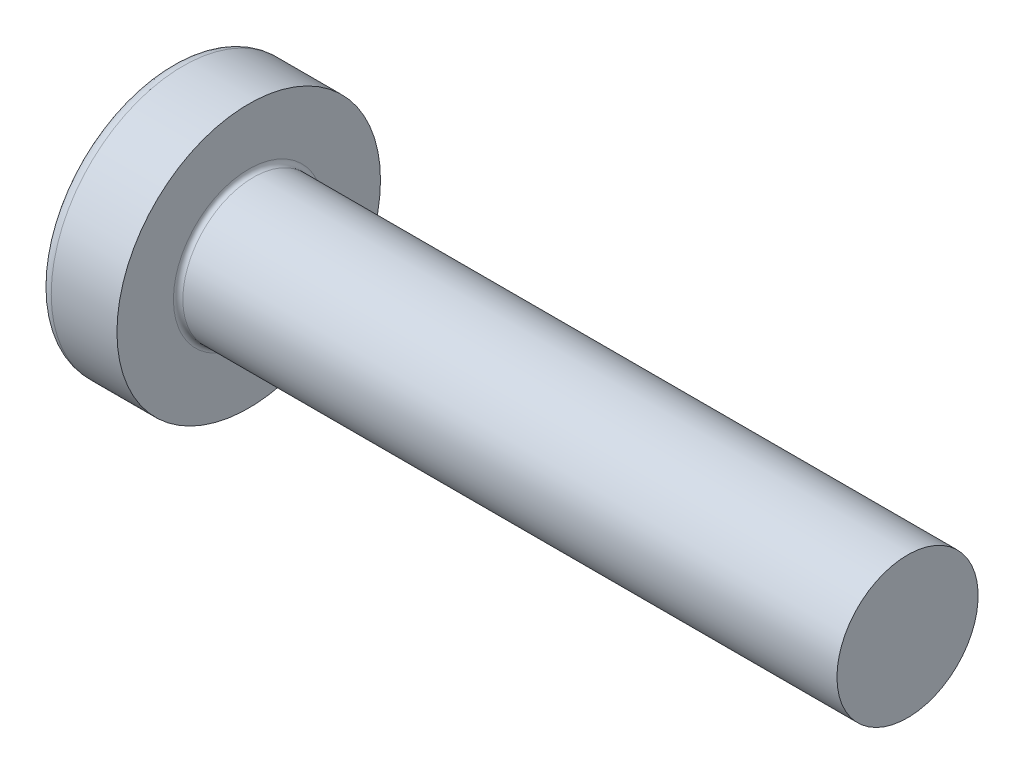
SolidWorks part; units mm, degrees
ref_plane "Plane1" through (0, 0, 0) normal (0, 0, 1) x (1, 0, 0)
ref_plane "Plane2" through (0, 0, 0) normal (0, 1, 0) x (1, 0, 0)
ref_plane "Plane3" through (0, 0, 0) normal (1, 0, 0) x (0, 0, -1)
sketch "BodySke" plane through (0, 0, 0) normal (0, 0, 1) x (1, 0, 0)
  line L0 (2.4, 1.5) -> (2.4, 2.8)
  line L1 (2.65, 6.35) -> (2.65, -3.175) construction
  line L2 (-25.4, 0) -> (127, 0) construction
  line L3 (16.4, 0) -> (0, 0)
  line L4 (2.4, 1.5) -> (16.4, 1.5)
  line L5 (16.4, 1.5) -> (16.4, 0)
  line L6 (1.0035, 2.8) -> (2.4, 2.8)
  line L8 (0.4, 6.35) -> (0.4, -3.175) construction
  arc A0 (0.7754, 2.6744) -> (0, 0) centre (5, 0) ccw
  arc A2 (0.7754, 2.6744) -> (1.0035, 2.8) centre (1.0035, 2.53) cw
  dimension "Head_crown_rad" = 5
  dimension "Head_fillet_rad" = 0.27
  dimension "Length" = 14
  dimension "Head_ht" = 2.4
  dimension "Head_dia" = 5.6
  dimension "Advance" = 0.5
  dimension "Thread_nom" = 16
  dimension "Diameter" = 3
revolve "Base-Revolve" add sketch "BodySke"
cosmetic thread "ThreadCosmetic" [suppressed]
fillet "Fillet1" radius 0.1 1 edges at (2.4, 0, 1.5)
sketch "Sketch3" plane through (0, 0, 0) normal (1, 0, 0) x (0, 0, -1)
  line L0 (0.37, -1.4) -> (-0.37, -1.4)
  line L1 (0.37, -1.4) -> (0.37, 1.4)
  line L2 (-0.37, 1.4) -> (0.37, 1.4)
  line L3 (-0.37, 1.4) -> (-0.37, -1.4)
  dimension "Cross_dia" = 2.8
  dimension "D1" = 1.4
  dimension "Cross_width" = 0.74
  dimension "D2" = 0.37
ref_plane "Plane4" through (1.75, 0, 0) normal (1, 0, 0) x (0, 0, -1)
sketch "Sketch4" plane through (1.75, 0, 0) normal (1, 0, 0) x (0, 0, -1)
  line L0 (0.37, -0.5275) -> (-0.37, -0.5275)
  line L1 (0.37, -0.5275) -> (0.37, 0.5275)
  line L2 (-0.37, 0.5275) -> (0.37, 0.5275)
  line L3 (-0.37, 0.5275) -> (-0.37, -0.5275)
  dimension "D1" = 0.74
  dimension "D2" = 1.055
  dimension "D3" = 0.37
  dimension "D4" = 0.5275
loft "Recess" cut profiles "Sketch3", "Sketch4"
pattern_circular "RecPat" count 2 every 90 about axis through (0, 0, 0) along (1, 0, 0) of "Recess"
sketch "RecCorSke" plane through (0, 0, 0) normal (0, 0, 1) x (1, 0, 0)
  line L0 (-3.175, 0) -> (15.875, 0) construction
  line L1 (-25.4, 0) -> (127, 0) construction
  line L2 (0, 0) -> (0, 0.6784)
  line L3 (0, 0.6784) -> (1.75, 0.556)
  line L4 (1.75, 0.556) -> (1.9307, 0)
  line L5 (1.9307, 0) -> (0, 0)
  dimension "Diameter" = 1.112
  dimension "Depth" = 1.75
  dimension "Draft_angle" = 4
  dimension "Bottom_angle" = 18
revolve "RecessCore" cut sketch "RecCorSke" angle 360 about L0
sketch "ThdSchSke" plane through (0, 0, 0) normal (0, 0, 1) x (1, 0, 0)
  line L0 (3.4, -1.2195) -> (3.2036, -1.5)
  line L1 (3.4, -1.2195) -> (3.5964, -1.5)
  line L2 (3.5964, -1.5) -> (3.5964, -1.875)
  line L3 (-3.175, 0) -> (5.1513, 0) construction
  line L5 (3.5964, -1.875) -> (3.2036, -1.875)
  line L6 (3.2036, -1.875) -> (3.2036, -1.5)
  dimension "Diameter" = 3
  dimension "SideAngle" = 55
  dimension "VeeAngle" = 70
  dimension "Thread_minor" = 2.439
  dimension "Overcut" = 3.75
  dimension "Start" = 3.4
revolve "ThreadSchematic" [suppressed] cut sketch "ThdSchSke" angle 360 about L3
pattern_linear "ThdSchPat" [suppressed]
equation "\"D1@Sketch3\" = \"Cross_dia@Sketch3\" / 2"
equation "\"D2@Sketch3\" = \"Cross_width@Sketch3\" / 2"
equation "\"Depth@RecCorSke\" = \"Cross_depth@Plane4\""
equation "\"D1@Sketch4\" = \"Cross_width@Sketch3\""
equation "\"D2@Sketch4\" = \"Cross_dia@Sketch3\" - 2.0 * \"Cross_depth@Plane4\" * tan(26.5  * 0.017453292)"
equation "\"D3@Sketch4\" = \"D1@Sketch4\" / 2"
equation "\"D4@Sketch4\" = \"D2@Sketch4\" / 2"
equation "\"Thread_length@ThreadCosmetic\" = ((sgn( (\"Length@BodySke\" - \"Advance@BodySke\" * 2.0 ) - \"Thread_nom@BodySke\" )-1)*( (\"Length@BodySke\" - \"Advance@BodySke\" * 2.0 ) - \"Thread_nom@BodySke\" ))/-2+ \"Thread_nom@BodySke\""
equation "\"Thread_minor@ThdSchSke\" = \"Thread_minor@ThreadCosmetic\""
equation "\"Diameter@ThdSchSke\" = \"Diameter@BodySke\""
equation "\"Overcut@ThdSchSke\" = \"Diameter@BodySke\" * 1.25"
equation "\"Start@ThdSchSke\" = \"Head_ht@BodySke\" + \"Length@BodySke\" - \"Thread_length@ThreadCosmetic\"  '---Non-countersunk---"
equation "\"Num_threads@ThdSchPat\" = int( \"Thread_length@ThreadCosmetic\" / \"Advance@BodySke\" + 0.999 )  + 1"
equation "\"Advance@ThdSchPat\" = \"Thread_length@ThreadCosmetic\" /  (\"Num_threads@ThdSchPat\" - 1) 'relax it"
